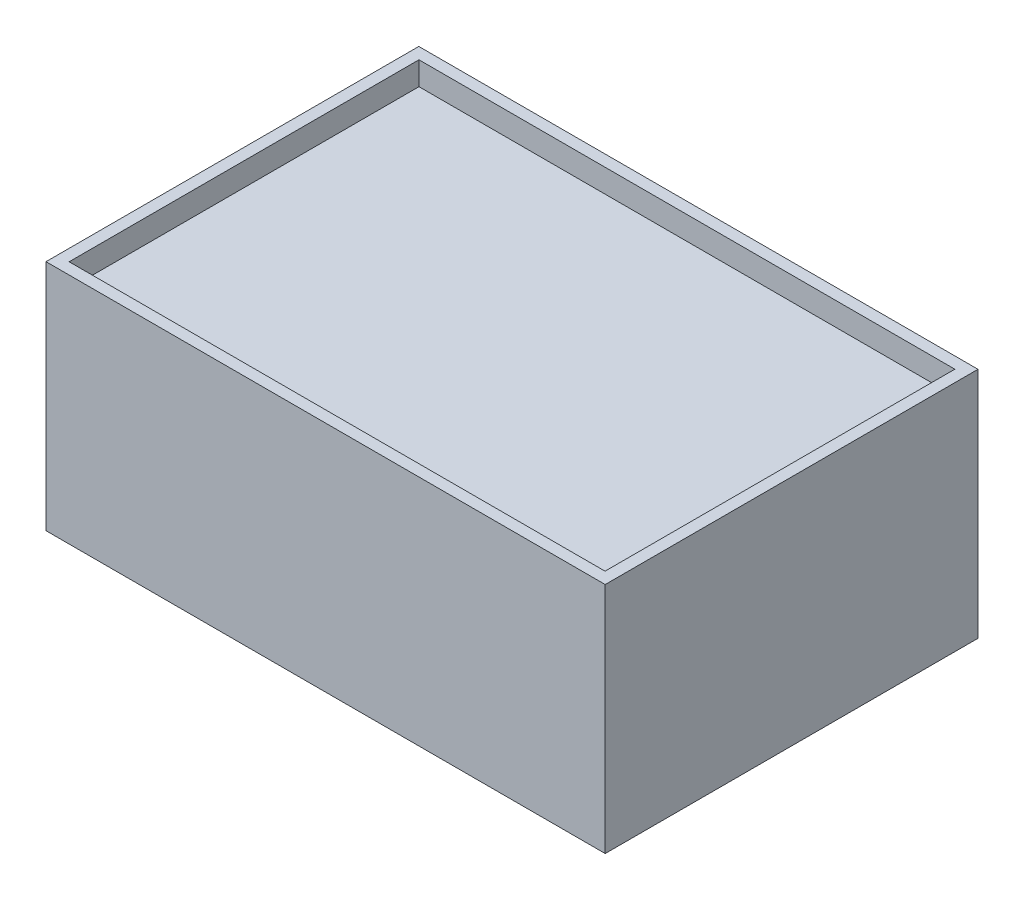
SolidWorks part; units mm, degrees
ref_plane "Front Plane" through (0, 0, 0) normal (0, 0, 1) x (1, 0, 0)
ref_plane "Top Plane" through (0, 0, 0) normal (0, 1, 0) x (1, 0, 0)
ref_plane "Right Plane" through (0, 0, 0) normal (1, 0, 0) x (0, 0, -1)
sketch "Sketch1" plane through (0, 0, 0) normal (0, 0, 1) x (1, 0, 0)
  line L1 (-76.2, 31.75) -> (76.2, 31.75)
  line L2 (-76.2, 31.75) -> (-76.2, -31.75)
  line L3 (-76.2, -31.75) -> (76.2, -31.75)
  line L4 (76.2, 31.75) -> (76.2, -31.75)
  line L5 (-76.2, 31.75) -> (76.2, -31.75) construction
  line L6 (-76.2, -31.75) -> (76.2, 31.75) construction
  point P0 (0, 0)
  dimension "D1" = 152.4
  dimension "D2" = 63.5
extrude "Boss-Extrude1" add sketch "Sketch1" against normal blind 101.6
sketch "Sketch3" plane through (0, 31.75, 0) normal (0, 1, 0) x (1, 0, 0)
  line L1 (-73.025, 98.47) -> (73.025, 98.47)
  line L2 (-73.025, 98.47) -> (-73.025, 3.13)
  line L3 (-73.025, 3.13) -> (73.025, 3.13)
  line L4 (73.025, 98.47) -> (73.025, 3.13)
  line L5 (-76.2, 101.6) -> (-76.2, 0) construction
  point P4 (0, 98.47)
  point P5 (-76.2, 50.8)
  point P7 (-73.025, 50.8)
  dimension "D1" = 146.05
  dimension "D2" = 95.34
extrude "Cut-Extrude1" cut sketch "Sketch3" against normal blind 6.35
mirror "Mirror1" about plane through (0, 0, 0) normal (0, 1, 0) of "Cut-Extrude1"
